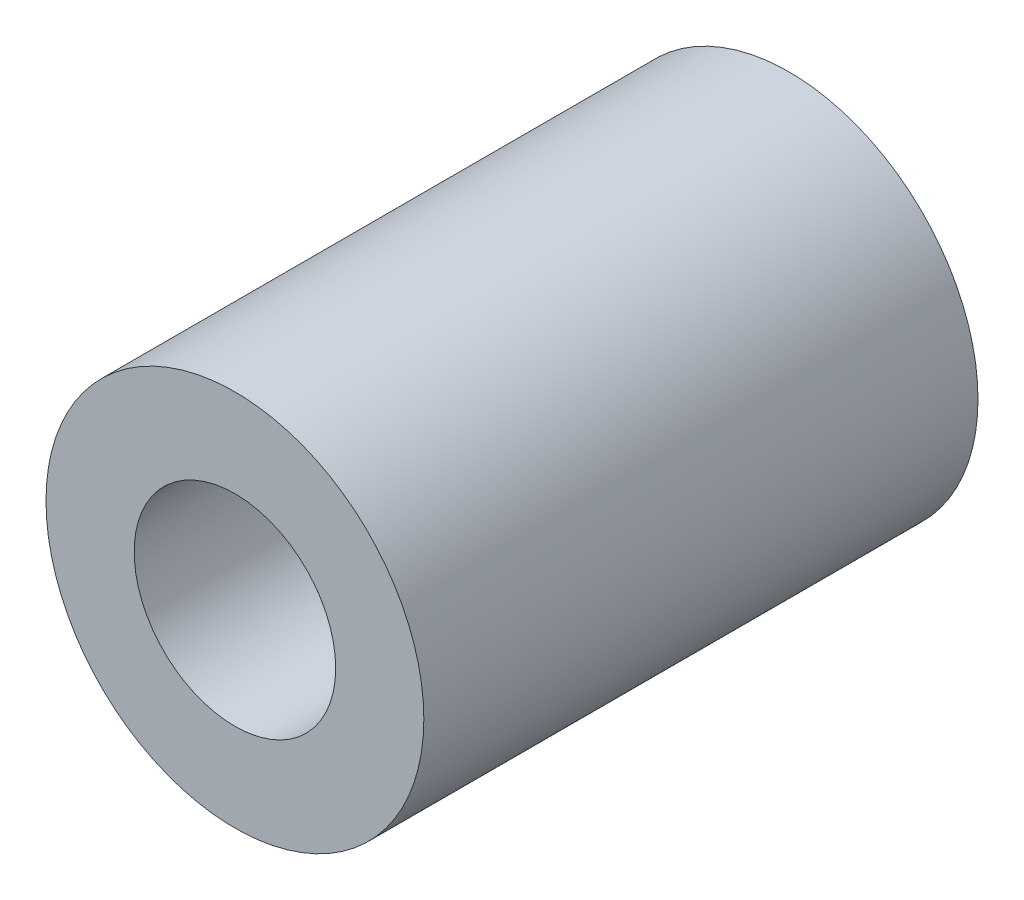
SolidWorks part; units mm, degrees
ref_plane "Plan de face" through (0, 0, 0) normal (0, 0, 1) x (1, 0, 0)
ref_plane "Plan de dessus" through (0, 0, 0) normal (0, 1, 0) x (1, 0, 0)
ref_plane "Plan de droite" through (0, 0, 0) normal (1, 0, 0) x (0, 0, -1)
sketch "Esquisse1" plane through (0, 0, 0) normal (0, 0, 1) x (1, 0, 0)
  circle A0 centre (0, 0) radius 4
  circle A1 centre (0, 0) radius 7.5
  dimension "D1" = 8
  dimension "D2" = 15
extrude "Boss.-Extru.1" add sketch "Esquisse1" along normal blind 22
